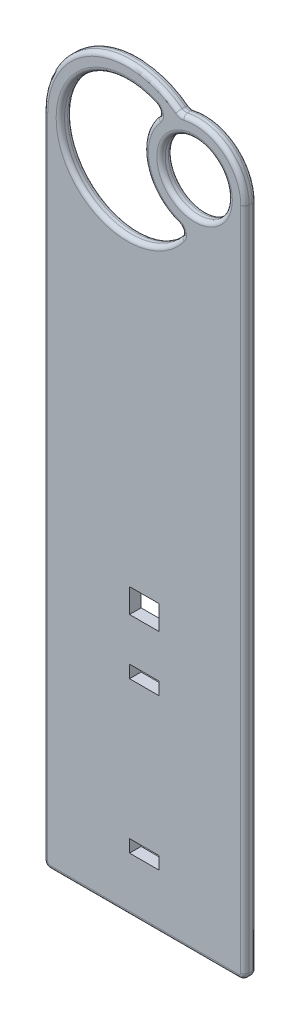
SolidWorks part; units mm, degrees
ref_plane "Front" through (0, 0, 0) normal (0, 0, 1) x (1, 0, 0)
ref_plane "Top" through (0, 0, 0) normal (0, 1, 0) x (1, 0, 0)
ref_plane "Right" through (0, 0, 0) normal (1, 0, 0) x (0, 0, -1)
sketch "Sketch1" plane through (0, 0, 0) normal (0, 0, 1) x (1, 0, 0)
  line L0 (-22.225, 330.2) -> (-22.225, 311.15)
  line L1 (-142.875, 0) -> (142.875, 0)
  line L2 (-152.4, 9.525) -> (-152.4, 990.6)
  line L3 (-22.225, 431.8) -> (22.225, 431.8)
  line L4 (152.4, 9.525) -> (152.4, 1016)
  line L5 (-22.225, 431.8) -> (-22.225, 395.2875)
  line L6 (-22.225, 82.55) -> (22.225, 82.55)
  line L7 (22.225, 431.8) -> (22.225, 395.2875)
  line L8 (-22.225, 311.15) -> (22.225, 311.15)
  line L9 (-22.225, 101.6) -> (-22.225, 82.55)
  line L10 (-22.225, 101.6) -> (22.225, 101.6)
  line L11 (22.225, 101.6) -> (22.225, 82.55)
  line L12 (-22.225, 395.2875) -> (22.225, 395.2875)
  line L13 (22.225, 330.2) -> (22.225, 311.15)
  line L14 (-22.225, 330.2) -> (22.225, 330.2)
  arc A0 (17.2342, 1082.8219) -> (55.6169, 929.2908) centre (-25.4, 990.6) ccw
  circle A1 centre (76.2, 1016) radius 50.8
  arc A2 (51.1638, 1091.9261) -> (-152.4, 990.6) centre (-25.4, 990.6) ccw
  arc A3 (20.2331, 1067.7121) -> (51.1525, 944.0343) centre (76.2, 1016) ccw
  arc A4 (152.4, 1016) -> (59.0499, 1090.245) centre (76.2, 1016) ccw
  arc A5 (142.875, 0) -> (152.4, 9.525) centre (142.875, 9.525) ccw
  arc A6 (-142.875, 0) -> (-152.4, 9.525) centre (-142.875, 9.525) cw
  arc A7 (51.1638, 1091.9261) -> (59.0499, 1090.245) centre (56.9061, 1099.5256) ccw
  arc A8 (55.6169, 929.2908) -> (51.1525, 944.0343) centre (48.0216, 935.0386) ccw
  arc A9 (20.2331, 1067.7121) -> (17.2342, 1082.8219) centre (13.2372, 1074.1761) ccw
  point P15 (-152.4, 0)
  dimension "D4" = 203.2
  dimension "D5" = 101.6
  dimension "D6" = 127
  dimension "D7" = 304.8
  dimension "D9" = 9.525
  dimension "D1" = 990.6
  dimension "D2" = 1016
  dimension "D3" = 152.4
  dimension "D8" = 76.2
  dimension "D10" = 44.45
  dimension "D11" = 22.225
  dimension "D12" = 82.55
  dimension "D13" = 431.8
  dimension "D14" = 101.6
  dimension "D15" = 311.15
  dimension "D16" = 330.2
  dimension "D17" = 395.2875
extrude "Boss-Extrude1" add sketch "Sketch1" along normal blind 17.4625
fillet "Fillet1" radius 6.35 26 edges at (22.58, 1076.0304, 0) (2.2751, 997.5188, 0) (57.1378, 937.799, 0) (57.1378, 937.799, 17.4625) (-123.9665, 965.9584, 17.4625) (22.58, 1076.0304, 17.4625) (152.4, 512.7625, 0) (149.6102, 2.7898, 0) (0, 0, 0) (-149.6102, 2.7898, 0) (-152.4, 500.0625, 0) (-81.9924, 1104.2939, 0) (54.9202, 1090.2099, 0) (149.6102, 2.7898, 17.4625) (0, 0, 17.4625) (-149.6102, 2.7898, 17.4625) (-152.4, 500.0625, 17.4625) (-81.9924, 1104.2939, 17.4625) (54.9202, 1090.2099, 17.4625) (123.6321, 1075.6376, 17.4625) (-123.9665, 965.9584, 0) (2.2751, 997.5188, 17.4625) (127, 1016, 17.4625) (127, 1016, 0) (123.6321, 1075.6376, 0) (152.4, 512.7625, 17.4625)
